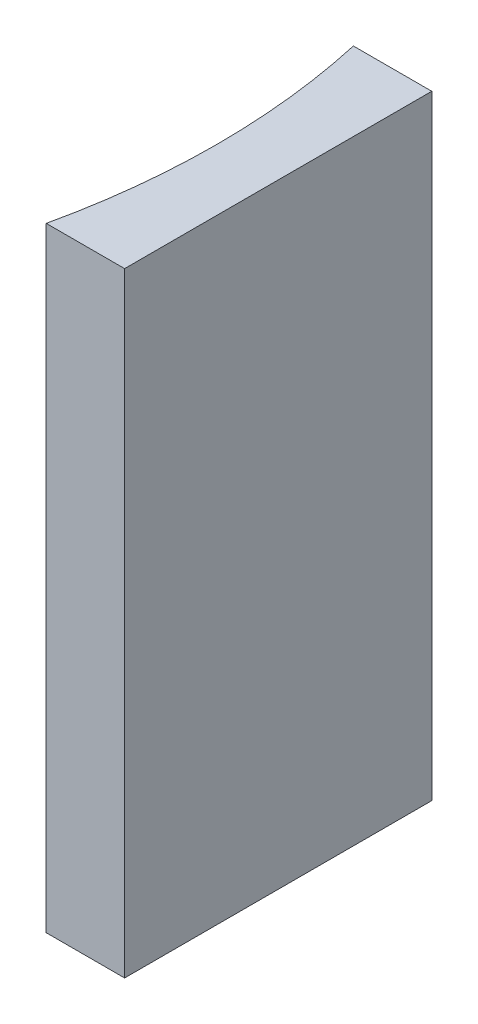
SolidWorks part; units mm, degrees
ref_plane "前视基准面" through (0, 0, 0) normal (0, 0, 1) x (1, 0, 0)
ref_plane "上视基准面" through (0, 0, 0) normal (0, 1, 0) x (1, 0, 0)
ref_plane "右视基准面" through (0, 0, 0) normal (1, 0, 0) x (0, 0, -1)
sketch "草图1" plane through (0, 0, 0) normal (0, 1, 0) x (1, 0, 0)
  line L0 (0, 0) -> (0, -10)
  line L1 (0, 0) -> (-2.552, 0)
  line L2 (0, -10) -> (-2.552, -10)
  line L3 (21.2259, -5) -> (-21.2259, -5) construction
  arc A0 (-2.552, -10) -> (-2.552, 0) centre (-24.92, -5) ccw
  point P7 (-2, -5)
  point P8 (0, -5)
  dimension "D2" = 22.92
  dimension "D3" = 2
  dimension "D1" = 10
extrude "凸台-拉伸1" add sketch "草图1" along normal blind 20
